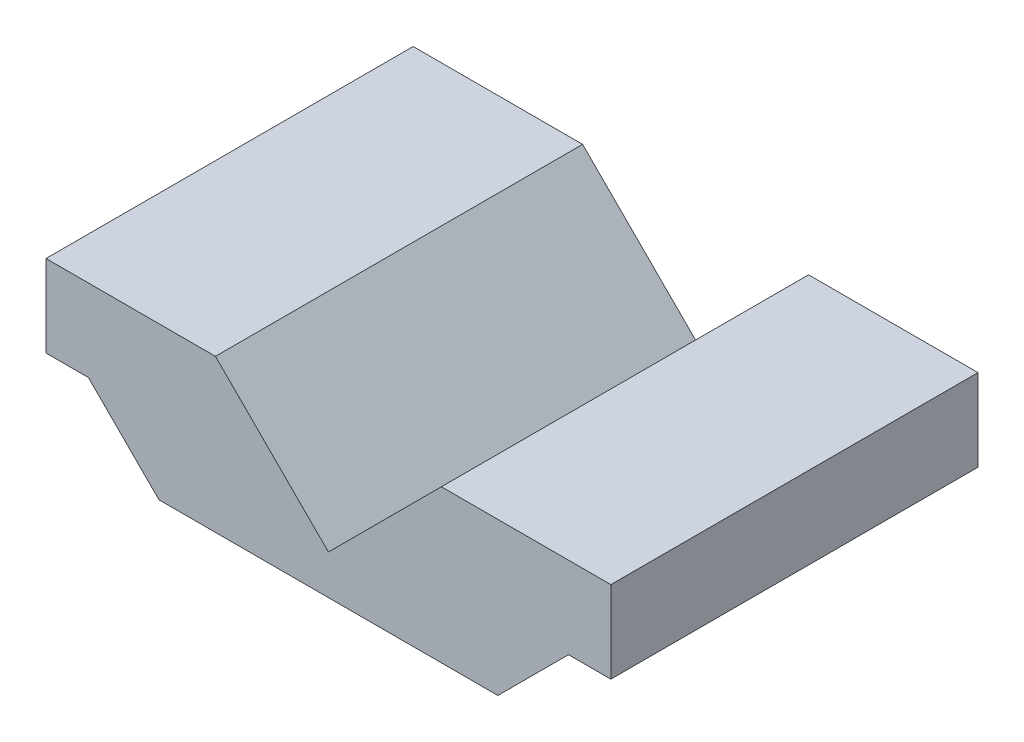
SolidWorks part; units mm, degrees
ref_plane "Alzado" through (0, 0, 0) normal (0, 0, 1) x (1, 0, 0)
ref_plane "Planta" through (0, 0, 0) normal (0, 1, 0) x (1, 0, 0)
ref_plane "Vista lateral" through (0, 0, 0) normal (1, 0, 0) x (0, 0, -1)
sketch "Croquis1" plane through (0, 0, 0) normal (0, 0, 1) x (1, 0, 0)
  line L0 (-30, 0) -> (30, 0)
  line L1 (30, 0) -> (42.5, 12.5)
  line L2 (30, 0) -> (53.4788, 0) construction
  line L3 (42.5, 12.5) -> (50, 12.5)
  line L4 (50, 12.5) -> (50, 27)
  line L5 (50, 27) -> (20, 27)
  line L6 (0, 0) -> (0, 40.8227) construction
  line L7 (20, 27) -> (0, 7)
  line L8 (-42.5, 12.5) -> (-50, 12.5)
  line L9 (-30, 0) -> (-42.5, 12.5)
  line L10 (-50, 12.5) -> (-50, 27)
  line L11 (-50, 27) -> (-20, 27)
  line L12 (-20, 27) -> (0, 7)
  dimension "D1" = 12.5
  dimension "D2" = 12.5
  dimension "D3" = 27
  dimension "D4" = 30
  dimension "D5" = 20
  dimension "D6" = 45
extrude "Saliente-Extruir1" add sketch "Croquis1" along normal mid plane 65
